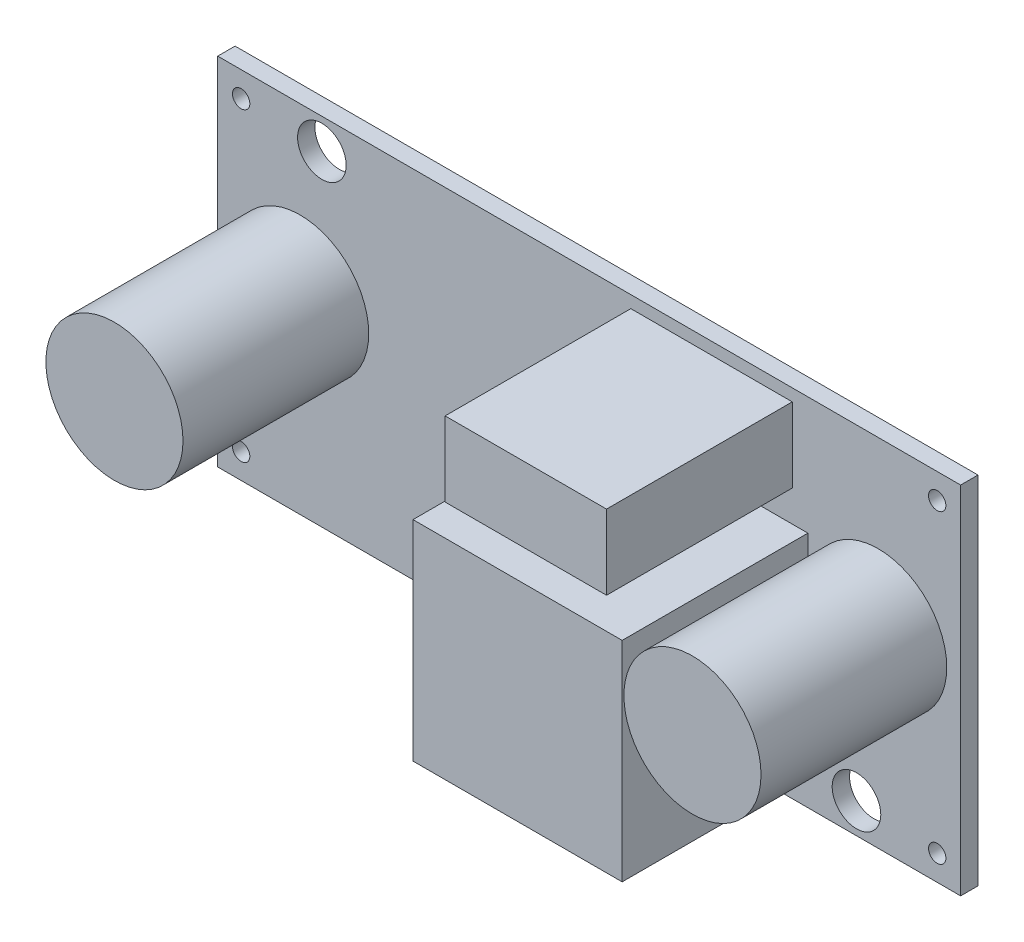
SolidWorks part; units mm, degrees
ref_plane "Front Plane" through (0, 0, 0) normal (0, 0, 1) x (1, 0, 0)
ref_plane "Top Plane" through (0, 0, 0) normal (0, 1, 0) x (1, 0, 0)
ref_plane "Right Plane" through (0, 0, 0) normal (1, 0, 0) x (0, 0, -1)
sketch "Sketch1" plane through (0, 0, 0) normal (0, 0, 1) x (1, 0, 0)
  line L1 (21.4, -10.25) -> (-21.4, -10.25)
  line L2 (21.4, -10.25) -> (21.4, 10.25)
  line L3 (21.4, 10.25) -> (-21.4, 10.25)
  line L4 (-21.4, -10.25) -> (-21.4, 10.25)
  line L5 (21.4, -10.25) -> (-21.4, 10.25) construction
  line L6 (21.4, 10.25) -> (-21.4, -10.25) construction
  circle A1 centre (15.4, -8.5) radius 1.4
  circle A2 centre (-15.4, 8.5) radius 1.4
  point P0 (0, 0)
  dimension "D4" = 2.8
  dimension "D6" = 2.8
  dimension "D1" = 42.8
  dimension "D2" = 20.5
  dimension "D3" = 6
  dimension "D5" = 1.75
  dimension "D7" = 6
  dimension "D8" = 1.75
extrude "Boss-Extrude1" add sketch "Sketch1" along normal blind 1
sketch "Sketch3" plane through (0, 0, 1) normal (0, 0, 1) x (1, 0, 0)
  line L0 (21.4, 10.25) -> (-21.4, 10.25) construction
  line L1 (11.7, 9.55) -> (2.4, 9.55)
  line L2 (11.7, 9.55) -> (11.7, 5.25)
  line L3 (11.7, 5.25) -> (2.4, 5.25)
  line L4 (2.4, 9.55) -> (2.4, 5.25)
  line L5 (11.7, 9.55) -> (2.4, 5.25) construction
  line L6 (11.7, 5.25) -> (2.4, 9.55) construction
  line L7 (12.6, 3.45) -> (0.55, 3.45)
  line L8 (12.6, 3.45) -> (12.6, -8.6)
  line L9 (12.6, -8.6) -> (0.55, -8.6)
  line L10 (0.55, 3.45) -> (0.55, -8.6)
  line L11 (12.6, 3.45) -> (0.55, -8.6) construction
  line L12 (12.6, -8.6) -> (0.55, 3.45) construction
  line L13 (-21.4, 10.25) -> (-21.4, -10.25) construction
  line L14 (21.4, -10.25) -> (21.4, 10.25) construction
  line L15 (-21.4, -10.25) -> (21.4, -10.25) construction
  circle A0 centre (16.65, 0.75) radius 3.95
  circle A1 centre (-16.65, 0.75) radius 3.95
  point P4 (7.05, 7.4)
  point P9 (6.575, -2.575)
  dimension "D1" = 7.9
  dimension "D2" = 9.5
  dimension "D3" = 4.75
  dimension "D4" = 4.75
  dimension "D5" = 9.3
  dimension "D6" = 4.3
  dimension "D7" = 9.7
  dimension "D8" = 0.7
  dimension "D9" = 12.05
  dimension "D10" = 12.05
  dimension "D11" = 1.65
  dimension "D12" = 8.8
extrude "Boss-Extrude2" add sketch "Sketch3" along normal blind 10.7
sketch "Sketch4" plane through (0, 0, 1) normal (0, 0, 1) x (1, 0, 0)
  line L1 (20.05, -8.8) -> (-20.05, -8.8) construction
  line L2 (20.05, -8.8) -> (20.05, 8.8) construction
  line L3 (20.05, 8.8) -> (-20.05, 8.8) construction
  line L4 (-20.05, -8.8) -> (-20.05, 8.8) construction
  line L5 (20.05, -8.8) -> (-20.05, 8.8) construction
  line L6 (20.05, 8.8) -> (-20.05, -8.8) construction
  circle A0 centre (-20.05, 8.8) radius 0.5
  circle A1 centre (-20.05, -8.8) radius 0.5
  circle A2 centre (20.05, -8.8) radius 0.5
  circle A3 centre (20.05, 8.8) radius 0.5
  point P0 (0, 0)
  dimension "D1" = 1
  dimension "D2" = 40.1
  dimension "D3" = 17.6
extrude "Cut-Extrude1" cut sketch "Sketch4" against normal through all
equation "\"D5@Sketch1\"=3.15-\"D4@Sketch1\"/2"
equation "\"D6@Sketch1\"=\"D4@Sketch1\""
equation "\"D7@Sketch1\"=\"D3@Sketch1\""
equation "\"D8@Sketch1\"=\"D5@Sketch1\""
equation "\"D2@Sketch3\"=5.55+\"D1@Sketch3\"/2"
equation "\"D3@Sketch3\"=.8+\"D1@Sketch3\"/2"
equation "\"D4@Sketch3\"=\"D3@Sketch3\""
